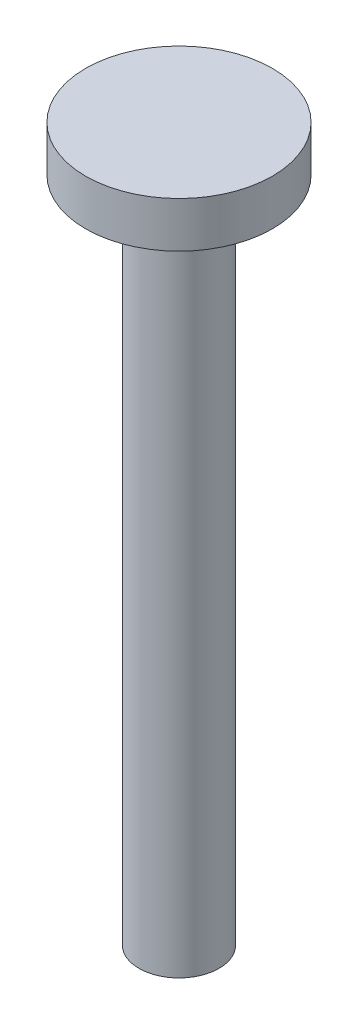
SolidWorks part; units mm, degrees
ref_plane "前视基准面" through (0, 0, 0) normal (0, 0, 1) x (1, 0, 0)
ref_plane "上视基准面" through (0, 0, 0) normal (0, 1, 0) x (1, 0, 0)
ref_plane "右视基准面" through (0, 0, 0) normal (1, 0, 0) x (0, 0, -1)
other "Configuration Table"
sketch "草图1" plane through (0, 0, 0) normal (0, 1, 0) x (1, 0, 0)
  circle A0 centre (0, 0) radius 3.5
  dimension "D1" = 7
extrude "凸台-拉伸1" add sketch "草图1" along normal blind 1.71
sketch "草图2" plane through (0, 0, 0) normal (0, -1, 0) x (1, 0, 0)
  circle A0 centre (0, 0) radius 1.5
  dimension "D1" = 3
extrude "凸台-拉伸2" add sketch "草图2" along normal blind 25
